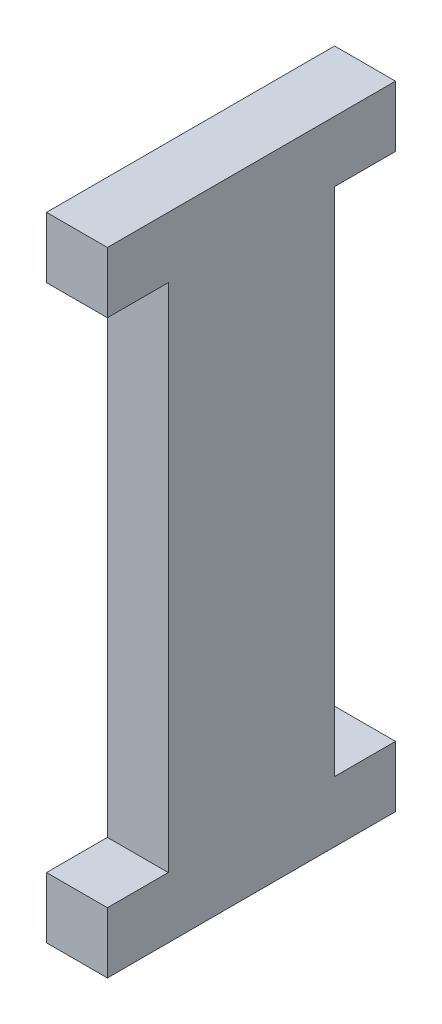
SolidWorks part; units mm, degrees
ref_plane "XY PLANE" through (0, 0, 0) normal (0, 0, 1) x (1, 0, 0)
ref_plane "XZ PLANE" through (0, 0, 0) normal (0, 1, 0) x (1, 0, 0)
ref_plane "YZ PLANE" through (0, 0, 0) normal (1, 0, 0) x (0, 0, -1)
sketch "Sketch1" plane through (0, 0, 0) normal (1, 0, 0) x (0, 0, -1)
  line L0 (11.83, 29.77) -> (11.83, 3.17)
  line L1 (0, 0) -> (15, 0)
  line L2 (0, 0) -> (0, 32.94)
  line L3 (0, 32.94) -> (15, 32.94)
  line L4 (15, 0) -> (15, 32.94)
  line L5 (0, 32.94) -> (3.17, 32.94)
  line L6 (0, 32.94) -> (0, 29.77)
  line L7 (0, 29.77) -> (3.17, 29.77)
  line L8 (3.17, 32.94) -> (3.17, 29.77)
  line L9 (0, 0) -> (3.17, 0)
  line L10 (0, 0) -> (0, 3.17)
  line L11 (0, 3.17) -> (3.17, 3.17)
  line L12 (3.17, 0) -> (3.17, 3.17)
  line L13 (15, 32.94) -> (11.83, 32.94)
  line L14 (15, 32.94) -> (15, 29.77)
  line L15 (15, 29.77) -> (11.83, 29.77)
  line L16 (11.83, 32.94) -> (11.83, 29.77)
  line L17 (15, 0) -> (11.83, 0)
  line L18 (15, 0) -> (15, 3.17)
  line L19 (15, 3.17) -> (11.83, 3.17)
  line L20 (11.83, 0) -> (11.83, 3.17)
  line L21 (3.17, 29.77) -> (3.17, 3.17)
  point P17 (0, 0)
  dimension "D1" = 32.94
  dimension "D2" = 3.17
  dimension "D3" = 3.17
  dimension "D4" = 15
extrude "Boss-Extrude1" add sketch "Sketch1" along normal blind 3.17 contours L3 L16 L15 L4 | L8 L3 L2 L7 | L1 L12 L11 L2 | L20 L1 L4 L19 | L8 L21 L12 L1 L20 L0 L16 L3
